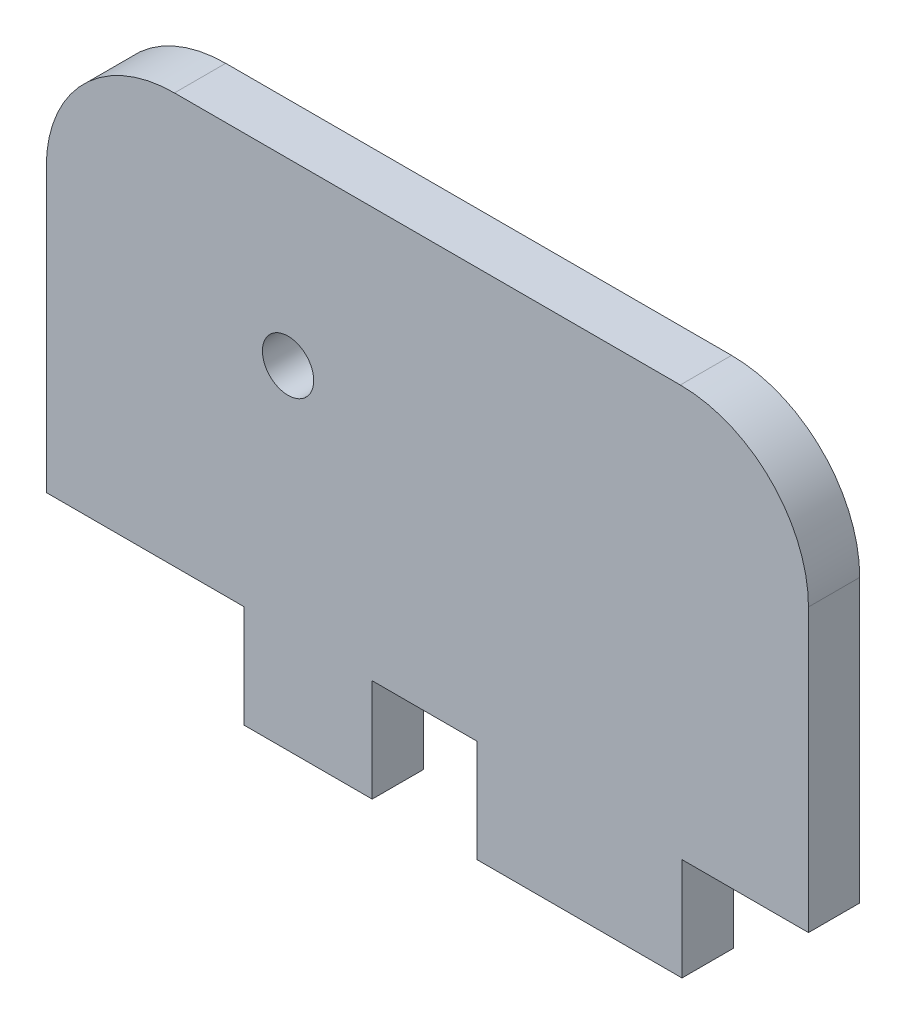
SolidWorks part; units mm, degrees
ref_plane "Front Plane" through (0, 0, 0) normal (0, 0, 1) x (1, 0, 0)
ref_plane "Top Plane" through (0, 0, 0) normal (0, 1, 0) x (1, 0, 0)
ref_plane "Right Plane" through (0, 0, 0) normal (1, 0, 0) x (0, 0, -1)
sketch "Sketch1" plane through (0, 0, 0) normal (0, 0, 1) x (1, 0, 0)
  line L0 (9.9327, -1) -> (14.8658, -1)
  line L1 (1.9327, -1) -> (-2.1519, -1)
  line L2 (-7.1519, -1) -> (-7.1519, -5)
  line L3 (-7.1519, -1) -> (-14.8658, -1)
  line L4 (-7.1519, -5) -> (-2.1519, -5)
  line L5 (-2.1519, -1) -> (-2.1519, -5)
  line L6 (9.9327, -1) -> (9.9327, -5)
  line L7 (9.9327, -5) -> (1.9327, -5)
  line L8 (1.9327, -5) -> (1.9327, -1)
  line L9 (-14.8658, 10) -> (-14.8658, -1)
  line L12 (14.8658, 10) -> (14.8658, -1)
  line L16 (9.8658, 15) -> (-9.8658, 15)
  arc A0 (14.8658, 10) -> (9.8658, 15) centre (9.8658, 10) ccw
  circle A1 centre (-5.4342, 8) radius 1
  arc A2 (-14.8658, 10) -> (-9.8658, 15) centre (-9.8658, 10) cw
  dimension "D1" = 2
  dimension "D3" = 1.9327
  dimension "D4" = 9.9327
  dimension "D5" = 14.8658
  dimension "D7" = 5.4342
  dimension "D2" = 5
  dimension "D8" = 7.1519
  dimension "D6" = 2.1519
  dimension "D9" = 14.8658
  dimension "D10" = 8
  dimension "D11" = 15
  dimension "D12" = 1
  dimension "D13" = 5
extrude "Boss-Extrude1" add sketch "Sketch1" along normal blind 2
